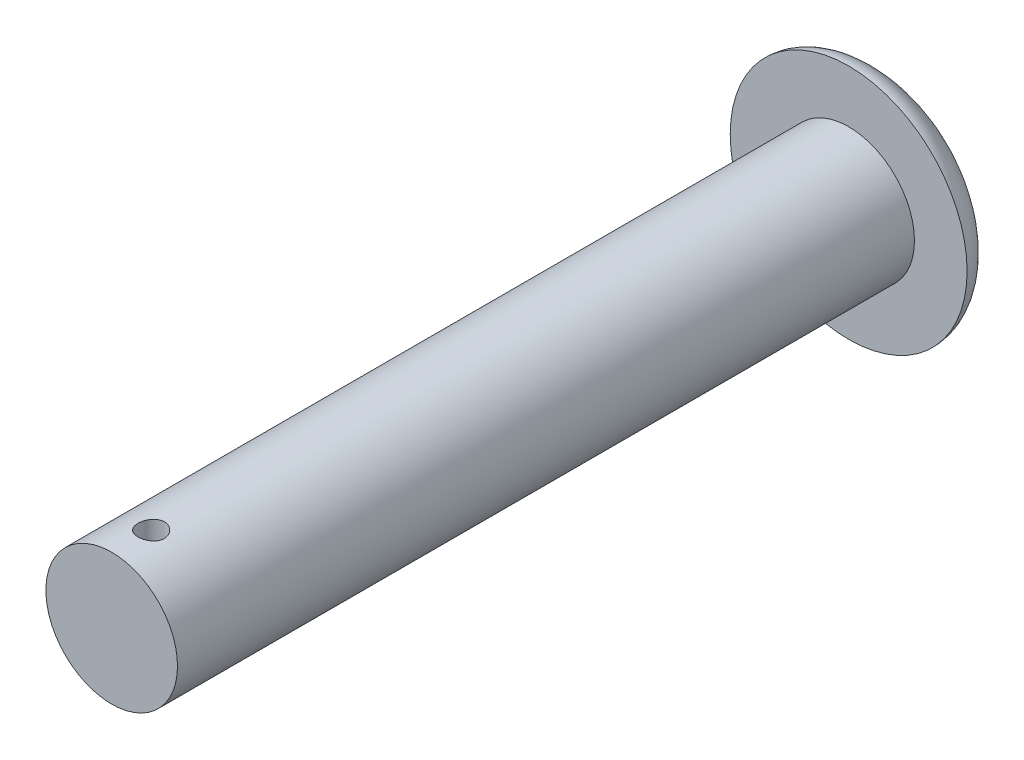
SolidWorks part; units mm, degrees
ref_plane "Front Plane" through (0, 0, 0) normal (0, 0, 1) x (1, 0, 0)
ref_plane "Top Plane" through (0, 0, 0) normal (0, 1, 0) x (1, 0, 0)
ref_plane "Right Plane" through (0, 0, 0) normal (1, 0, 0) x (0, 0, -1)
sketch "Sketch1" plane through (0, 0, 0) normal (0, 1, 0) x (1, 0, 0)
  line L0 (0, 0) -> (0, 30)
  line L3 (-4.5, 28) -> (-2.5, 28)
  line L4 (-2.5, 28) -> (-2.5, 0)
  line L5 (-2.5, 0) -> (0, 0)
  ellipse E0 centre (0, 28) end of major axis (-4.5, 28) minor radius 2 (0, 30) -> (-4.5, 28) ccw
  dimension "D1" = 2.5
  dimension "D2" = 30
  dimension "D3" = 2
  dimension "D4" = 2
revolve "Revolve1" add sketch "Sketch1" angle 360 about L0
sketch "Sketch2" plane through (0, 0, 0) normal (0, 1, 0) x (1, 0, 0)
  circle A0 centre (0, 1.5) radius 0.5
  dimension "D1" = 1
  dimension "D2" = 1.5
extrude "Cut-Extrude1" cut sketch "Sketch2" against normal through all both and the other way through all contours A0
